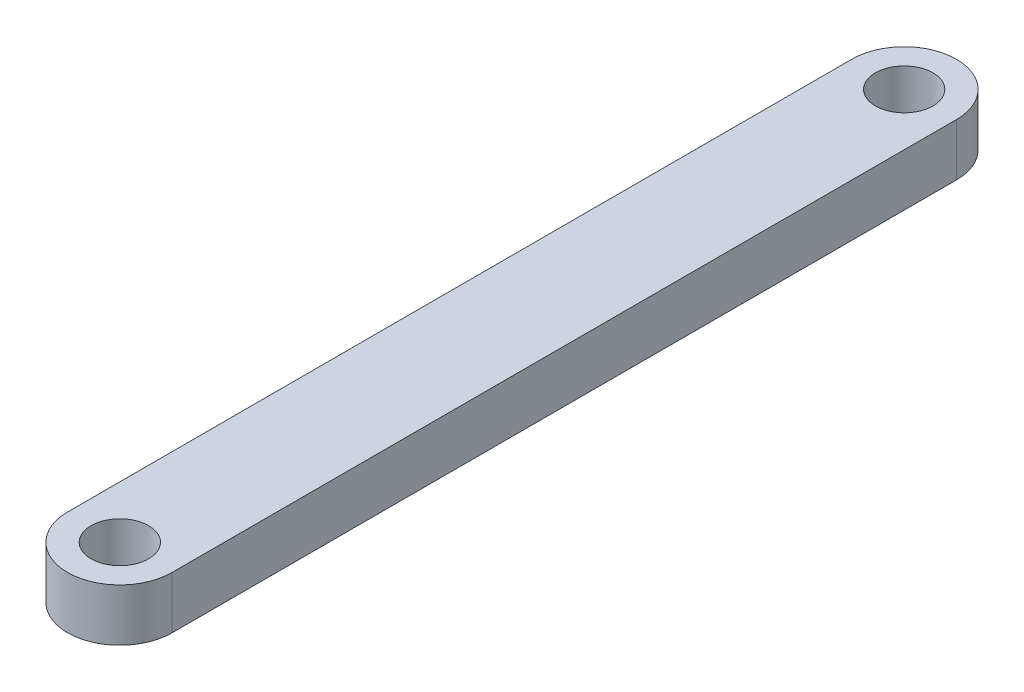
SolidWorks part; units mm, degrees
ref_plane "Front Plane" through (0, 0, 0) normal (0, 0, 1) x (1, 0, 0)
ref_plane "Top Plane" through (0, 0, 0) normal (0, 1, 0) x (1, 0, 0)
ref_plane "Right Plane" through (0, 0, 0) normal (1, 0, 0) x (0, 0, -1)
sketch "Sketch1" plane through (0, 0, 0) normal (0, 1, 0) x (1, 0, 0)
  line L0 (0, 0) -> (0, 75)
  line L1 (0, 75) -> (0, 0) construction
  line L2 (5, 75) -> (5, 0)
  line L3 (-5, 75) -> (-5, 0)
  circle A0 centre (0, 75) radius 2.75
  circle A1 centre (0, 0) radius 2.75
  arc A2 (5, 75) -> (-5, 75) centre (0, 75) ccw
  arc A3 (-5, 0) -> (5, 0) centre (0, 0) ccw
  point P5 (0, 37.5)
extrude "Boss-Extrude1" add sketch "Sketch1" along normal blind 5
